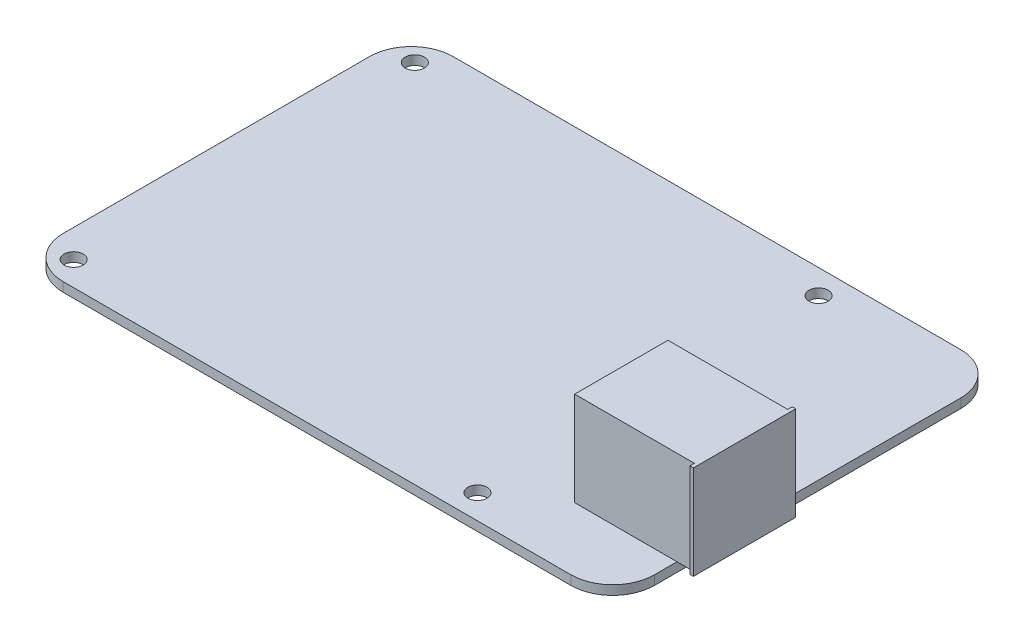
SolidWorks part; units mm, degrees
ref_plane "Alzado" through (0, 0, 0) normal (0, 0, 1) x (1, 0, 0)
ref_plane "Planta" through (0, 0, 0) normal (0, 1, 0) x (1, 0, 0)
ref_plane "Vista lateral" through (0, 0, 0) normal (1, 0, 0) x (0, 0, -1)
sketch "Croquis1" plane through (0, 0, 0) normal (0, 1, 0) x (1, 0, 0)
  line L1 (-42.46, 28) -> (42.46, 28)
  line L2 (-42.46, 28) -> (-42.46, -28)
  line L3 (-42.46, -28) -> (42.46, -28)
  line L4 (42.46, 28) -> (42.46, -28)
  line L5 (-42.46, 28) -> (42.46, -28) construction
  line L6 (-42.46, -28) -> (42.46, 28) construction
  point P0 (0, 0)
  dimension "D1" = 84.92
  dimension "D2" = 56
extrude "Saliente-Extruir1" add sketch "Croquis1" along normal blind 1.33
fillet "Redondeo1" radius 6 4 edges at (42.46, 0.665, -28) (42.46, 0.665, 28) (-42.46, 0.665, -28) (-42.46, 0.665, 28)
sketch "Croquis2" plane through (0, 1.33, 0) normal (0, 1, 0) x (1, 0, 0)
  line L0 (-42.46, 0) -> (42.46, 0) construction
  line L1 (-38.46, 24.5) -> (19.54, 24.5) construction
  line L2 (-38.46, 24.5) -> (-38.46, -24.5) construction
  line L3 (-38.46, -24.5) -> (19.54, -24.5) construction
  line L4 (19.54, 24.5) -> (19.54, -24.5) construction
  line L5 (-42.46, 22) -> (-42.46, -22) construction
  line L6 (42.46, -22) -> (42.46, 22) construction
  circle A0 centre (-38.46, 24.5) radius 1.375
  circle A1 centre (-38.46, -24.5) radius 1.375
  circle A2 centre (19.54, -24.5) radius 1.375
  circle A3 centre (19.54, 24.5) radius 1.375
  dimension "D1" = 2.75
  dimension "D2" = 58
  dimension "D3" = 49
  dimension "D4" = 4
extrude "Cortar-Extruir1" cut sketch "Croquis2" against normal blind 1.33
sketch "Croquis3" plane through (0, 1.33, 0) normal (0, 1, 0) x (1, 0, 0)
  line L0 (42.46, -22) -> (42.46, 22) construction
  line L1 (45.46, -18.7621) -> (45.46, -19.4121)
  line L2 (44.96, -4.7121) -> (45.46, -4.7121)
  line L3 (44.96, -4.7121) -> (44.96, -5.3621)
  line L4 (44.96, -19.4121) -> (45.46, -19.4121)
  line L5 (45.46, -4.7121) -> (45.46, -5.3621)
  line L6 (44.96, -18.7621) -> (44.96, -19.4121)
  line L7 (27.76, -12.0621) -> (45.46, -12.0621) construction
  line L11 (27.76, -5.3621) -> (44.96, -5.3621)
  line L12 (27.76, -5.3621) -> (27.76, -18.7621)
  line L13 (27.76, -18.7621) -> (44.96, -18.7621)
  line L14 (45.46, -5.3621) -> (45.46, -18.7621)
  dimension "D1" = 17.7
  dimension "D2" = 13.4
  dimension "D3" = 3
  dimension "D4" = 14.7
  dimension "D5" = 0.5
extrude "Saliente-Extruir2" add sketch "Croquis3" along normal blind 13.5
